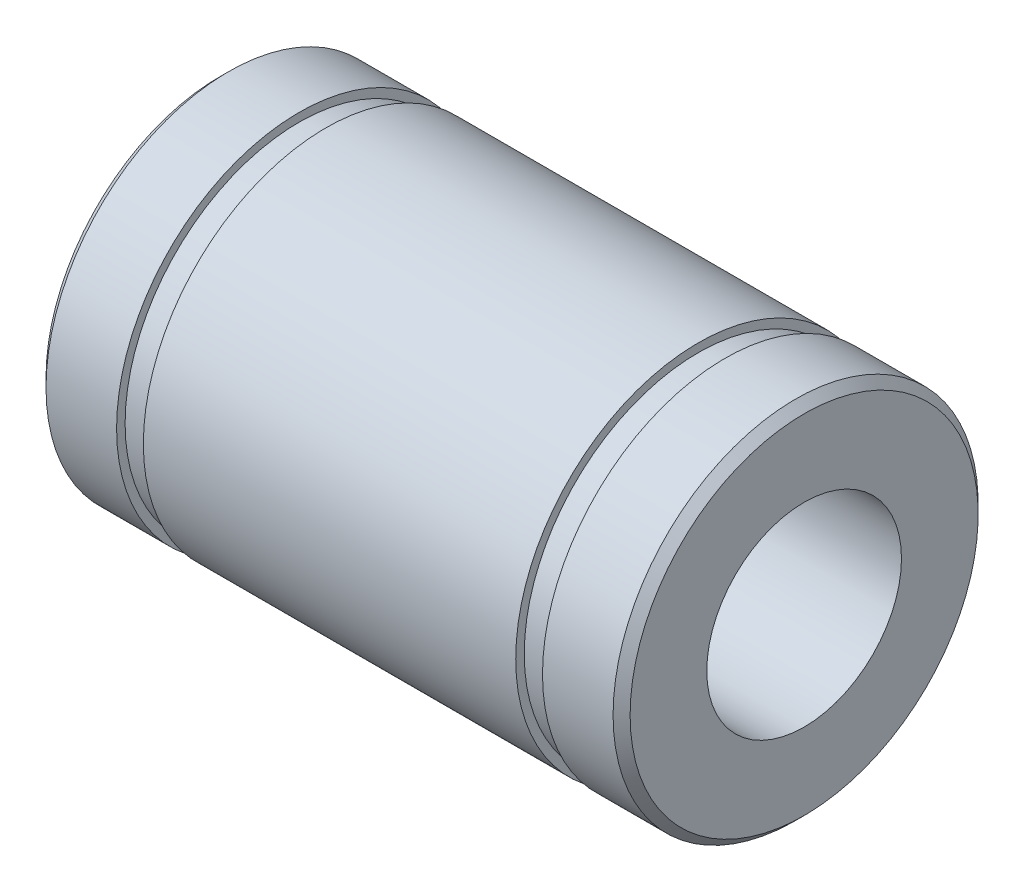
SolidWorks part; units mm, degrees
material "Легированная сталь"
ref_plane "Спереди" through (0, 0, 0) normal (0, 0, 1) x (1, 0, 0)
ref_plane "Сверху" through (0, 0, 0) normal (0, 1, 0) x (1, 0, 0)
ref_plane "Справа" through (0, 0, 0) normal (1, 0, 0) x (0, 0, -1)
other "Configuration Table"
sketch "Эскиз1" plane through (0, 0, 0) normal (0, 1, 0) x (1, 0, 0)
  line L0 (-14.548, 0) -> (15.9128, 0) construction
  line L1 (-11.65, -7.5) -> (-8.75, -7.5)
  line L2 (-12, -7.15) -> (-12, -4)
  line L4 (12, -7.15) -> (12, -4)
  line L5 (-11.7846, -7.3654) -> (0, 0) construction
  line L6 (0, 0) -> (11.7846, -7.3654) construction
  line L7 (-8.75, -7.15) -> (-7.65, -7.15)
  line L8 (-7.65, -7.15) -> (-7.65, -7.5)
  line L9 (-8.75, -7.15) -> (-8.75, -7.5)
  line L10 (8.75, -7.5) -> (8.75, -7.15)
  line L11 (8.75, -7.15) -> (7.65, -7.15)
  line L12 (7.65, -7.15) -> (7.65, -7.5)
  line L13 (0, 0) -> (0, -9.4202) construction
  line L14 (-7.65, -7.5) -> (7.65, -7.5)
  line L15 (8.75, -7.5) -> (11.65, -7.5)
  line L16 (-12, -7.15) -> (-11.65, -7.5)
  line L17 (12, -7.15) -> (11.65, -7.5)
  line L18 (-12, -4) -> (12, -4)
  point P0 (0, 0)
  point P1 (-8.2, -7.15)
  point P3 (0, -4)
  dimension "D2" = 135
  dimension "D3" = 1.1
  dimension "D4" = 17.5
  dimension "D5" = 1.1
  dimension "D6" = 7.15
  dimension "D7" = 7.15
  dimension "D8" = 0.495
  dimension "D9" = 3.15
  dimension "D10" = 12
  dimension "D11" = 135
  dimension "D12" = 2.9
  dimension "D13" = 4
revolve "Повернуть1" add sketch "Эскиз1" angle 360 about L0
sketch "Эскиз2" plane through (-12, 0, 0) normal (-1, 0, 0) x (0, 0, 1)
  circle A0 centre (0, 0) radius 4 construction
  point P0 (0, -4)
